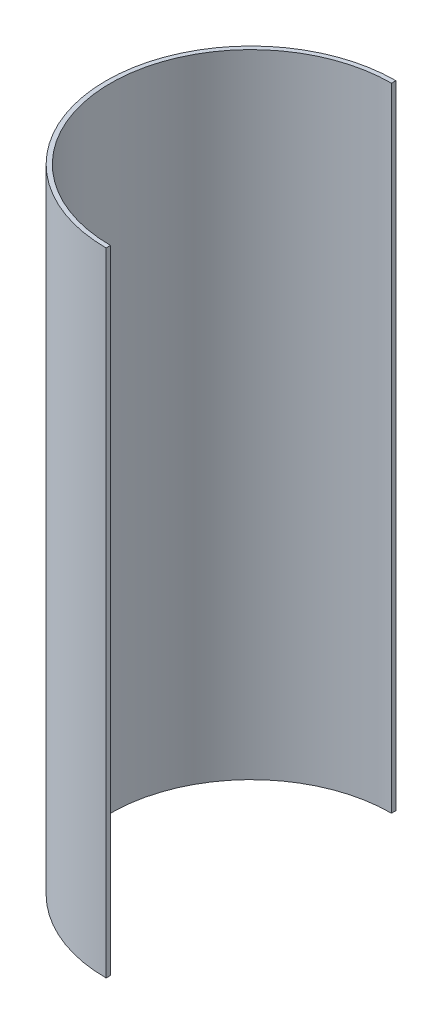
SolidWorks part; units mm, degrees
ref_plane "Front Plane" through (0, 0, 0) normal (0, 0, 1) x (1, 0, 0)
ref_plane "Top Plane" through (0, 0, 0) normal (0, 1, 0) x (1, 0, 0)
ref_plane "Right Plane" through (0, 0, 0) normal (1, 0, 0) x (0, 0, -1)
sketch "Sketch1" plane through (0, 0, 0) normal (0, 1, 0) x (1, 0, 0)
  line L3 (0, 104.775) -> (0, 101.6)
  line L5 (0, -101.6) -> (0, -104.775)
  arc A1 (0, 101.6) -> (0, -101.6) centre (0, 0) ccw
  arc A3 (0, 104.775) -> (0, -104.775) centre (0, 0) ccw
  dimension "D1" = 101.6
extrude "Boss-Extrude1" add sketch "Sketch1" along normal blind 457.2
